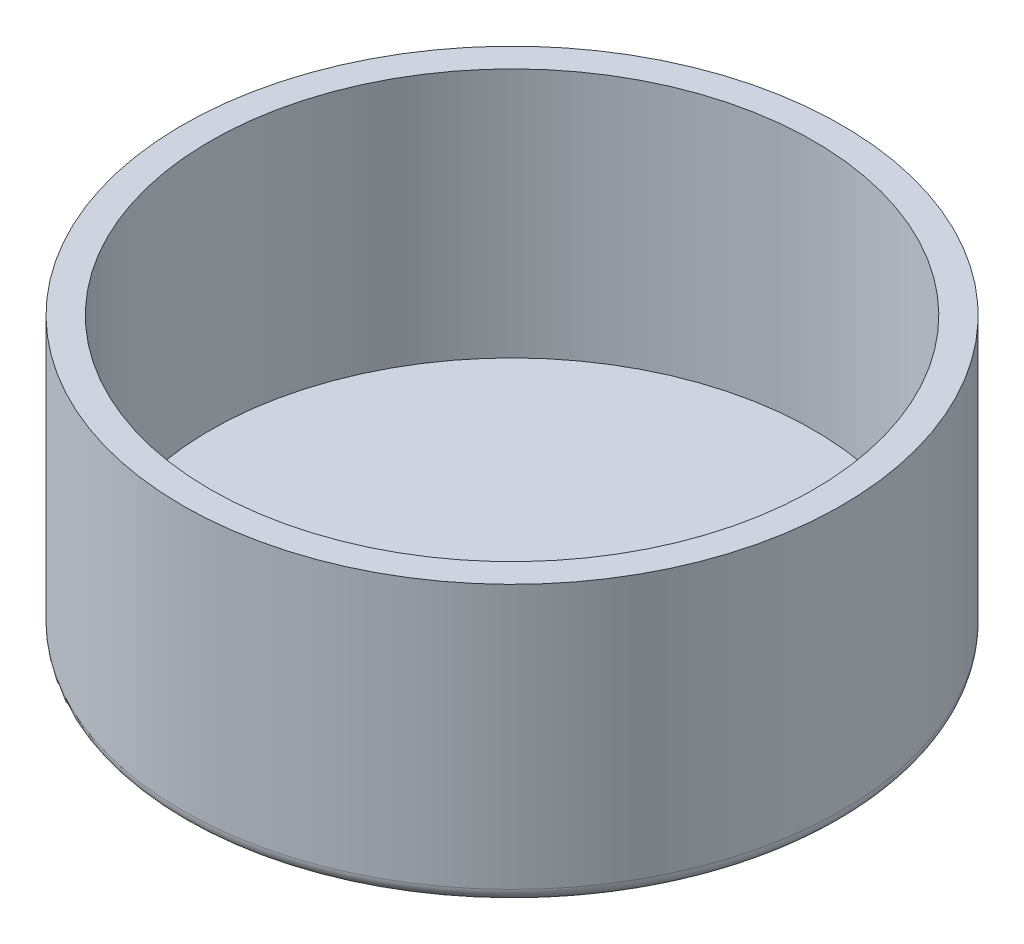
SolidWorks part; units mm, degrees
ref_plane "Front Plane" through (0, 0, 0) normal (0, 0, 1) x (1, 0, 0)
ref_plane "Top Plane" through (0, 0, 0) normal (0, 1, 0) x (1, 0, 0)
ref_plane "Right Plane" through (0, 0, 0) normal (1, 0, 0) x (0, 0, -1)
sketch "Sketch1" plane through (0, 0, 0) normal (0, 1, 0) x (1, 0, 0)
  circle A0 centre (0, 0) radius 11.85
  dimension "D1" = 23.7
extrude "Boss-Extrude1" add sketch "Sketch1" along normal blind 1
sketch "Sketch2" plane through (0, 1, 0) normal (0, 1, 0) x (1, 0, 0)
  circle A0 centre (0, 0) radius 11.85
  circle A1 centre (0, 0) radius 10.85
  circle A2 centre (0, 0) radius 11.85 construction
  dimension "D1" = 1
extrude "Boss-Extrude2" add sketch "Sketch2" along normal blind 9
fillet "Fillet1" radius 0.5 1 edges at (0, 0, 11.85)
